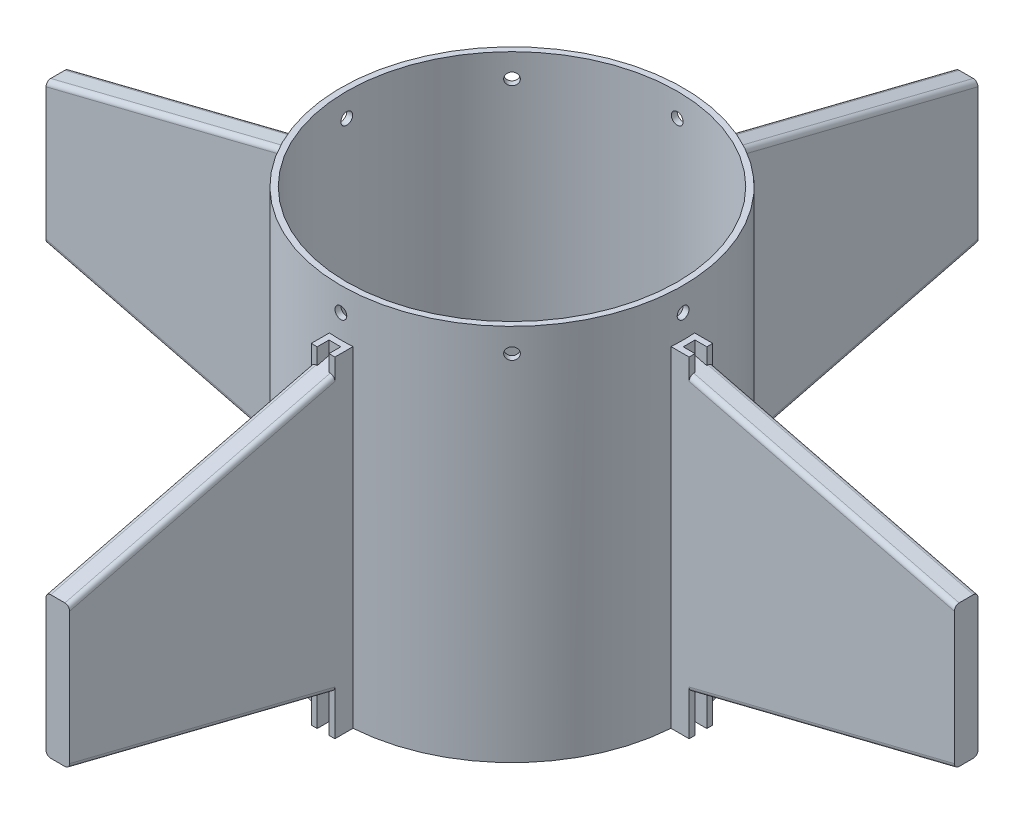
SolidWorks part; units mm, degrees
ref_plane "Front Plane" through (0, 0, 0) normal (0, 0, 1) x (1, 0, 0)
ref_plane "Top Plane" through (0, 0, 0) normal (0, 1, 0) x (1, 0, 0)
ref_plane "Right Plane" through (0, 0, 0) normal (1, 0, 0) x (0, 0, -1)
sketch "Sketch1" plane through (0, 0, 0) normal (0, 1, 0) x (1, 0, 0)
  circle A0 centre (0, 0) radius 92.075
  circle A1 centre (0, 0) radius 88.9
  dimension "D1" = 184.15
  dimension "D2" = 177.8
extrude "Base Shell" add sketch "Sketch1" along normal blind 203.2
sketch "Sketch2" plane through (0, 0, 0) normal (0, -1, 0) x (1, 0, 0)
  circle A1 centre (0, 0) radius 69.85 construction
  circle A2 centre (0, 0) radius 88.9 construction
  circle A3 centre (0, 0) radius 88.9
  arc A4 (-78.8035, -9.5078) -> (-9.5078, -78.8035) centre (0, 0) ccw
  circle A5 centre (0, 79.375) radius 3.175
  circle A6 centre (79.375, 0) radius 3.175
  circle A7 centre (0, -79.375) radius 3.175
  circle A8 centre (-79.375, 0) radius 3.175
  arc A9 (-9.5078, 78.8035) -> (9.5078, 78.8035) centre (0, 79.375) ccw
  arc A10 (78.8035, 9.5078) -> (78.8035, -9.5078) centre (79.375, 0) ccw
  arc A11 (9.5078, -78.8035) -> (-9.5078, -78.8035) centre (0, -79.375) ccw
  arc A12 (-78.8035, -9.5078) -> (-78.8035, 9.5078) centre (-79.375, 0) ccw
  arc A13 (-9.5078, 78.8035) -> (-78.8035, 9.5078) centre (0, 0) ccw
  arc A14 (78.8035, 9.5078) -> (9.5078, 78.8035) centre (0, 0) ccw
  arc A15 (9.5078, -78.8035) -> (78.8035, -9.5078) centre (0, 0) ccw
  point P18 (0, 0)
  point P26 (0, 0)
  dimension "D1" = 139.7
extrude "Bolt Insert" add sketch "Sketch2" against normal blind 6.35
sketch "Sketch3" plane through (0, 0, 0) normal (0, 1, 0) x (1, 0, 0)
  line L0 (-6.35, 0) -> (6.35, 0)
  line L7 (-6.35, 101.6) -> (-3.175, 101.6)
  line L9 (0, 101.6) -> (0, 92.075) construction
  line L10 (-6.35, 101.6) -> (-5.7435, 91.8957) construction
  line L11 (-6.35, 91.8558) -> (-6.35, 101.6)
  line L12 (5.7435, 91.8957) -> (6.35, 101.6) construction
  line L14 (6.35, 91.8558) -> (6.35, 101.6)
  line L15 (-3.175, 101.6) -> (-3.175, 95.25)
  line L16 (-3.175, 95.25) -> (3.175, 95.25)
  line L17 (3.175, 101.6) -> (3.175, 95.25)
  line L18 (0, 101.6) -> (3.175, 95.25) construction
  line L19 (-3.175, 95.25) -> (0, 101.6) construction
  line L20 (3.175, 101.6) -> (6.35, 101.6)
  circle A2 centre (0, 0) radius 92.075 construction
  arc A3 (6.35, 91.8558) -> (-6.35, 91.8558) centre (0, 0) ccw
  point P1 (0, 101.6)
  dimension "D1" = 12.7
  dimension "D2" = 101.6
  dimension "D3" = 6.35
  dimension "D4" = 3.175
  dimension "D5" = 3.175
extrude "Fin Bracket" add sketch "Sketch3" along normal blind 177.8 contours A3 L14 L20 L17 L16 L15 L7 L11
pattern_circular "CirPattern1" count 4 over 360 about axis through (0, 0, 0) along (0, 1, 0) of "Fin Bracket"
sketch "Sketch4" plane through (0, 0, 0) normal (0, 0, 1) x (1, 0, 0)
  line L0 (0, 0) -> (95.25, 0) construction
  line L1 (91.8558, 19.05) -> (91.8558, 171.45)
  line L2 (91.8558, 95.25) -> (244.2558, 95.25) construction
  line L6 (91.8558, 177.8) -> (91.8558, 0) construction
  line L8 (91.8558, 19.05) -> (91.8558, 171.45)
  line L14 (244.2558, 133.35) -> (91.8558, 171.45)
  line L15 (244.2558, 57.15) -> (244.2558, 133.35)
  line L16 (91.8558, 19.05) -> (244.2558, 57.15)
  point P6 (0, 0)
  point P7 (244.2558, 95.25)
  dimension "D1" = 76.2
  dimension "D2" = 152.4
  dimension "D3" = 152.4
  dimension "D4" = 6.35
extrude "Base Fin" add sketch "Sketch4" along normal mid plane 12.7
pattern_circular "Fin Pattern" count 4 over 360 about axis through (0, 0, 0) along (0, 1, 0) of "Base Fin"
fillet "Fin Fillets" radius 2.54 16 edges at (172.9279, 39.318, -6.35) (172.9279, 151.182, -6.35) (172.9279, 151.182, 6.35) (172.9279, 39.318, 6.35) (6.35, 39.318, 172.9279) (6.35, 151.182, 172.9279) (-6.35, 151.182, 172.9279) (-6.35, 39.318, 172.9279) (-172.9279, 39.318, 6.35) (-172.9279, 151.182, 6.35) (-172.9279, 151.182, -6.35) (-172.9279, 39.318, -6.35) (-6.35, 39.318, -172.9279) (-6.35, 151.182, -172.9279) (6.35, 151.182, -172.9279) (6.35, 39.318, -172.9279)
sketch "Sketch5" plane through (0, 0, 0) normal (0, 0, 1) x (1, 0, 0)
  line L0 (0, 203.2) -> (0, 177.8) construction
  line L1 (92.075, 203.2) -> (-92.075, 203.2) construction
  line L2 (6.35, 177.8) -> (-6.35, 177.8) construction
  circle A0 centre (0, 190.5) radius 3.175
  dimension "D1" = 6.35
extrude "Cut-Extrude1" cut sketch "Sketch5" against normal through all
pattern_circular "CirPattern2" count 8 over 360 about axis through (0, 203.2, 0) along (0, 1, 0) of "Cut-Extrude1"
